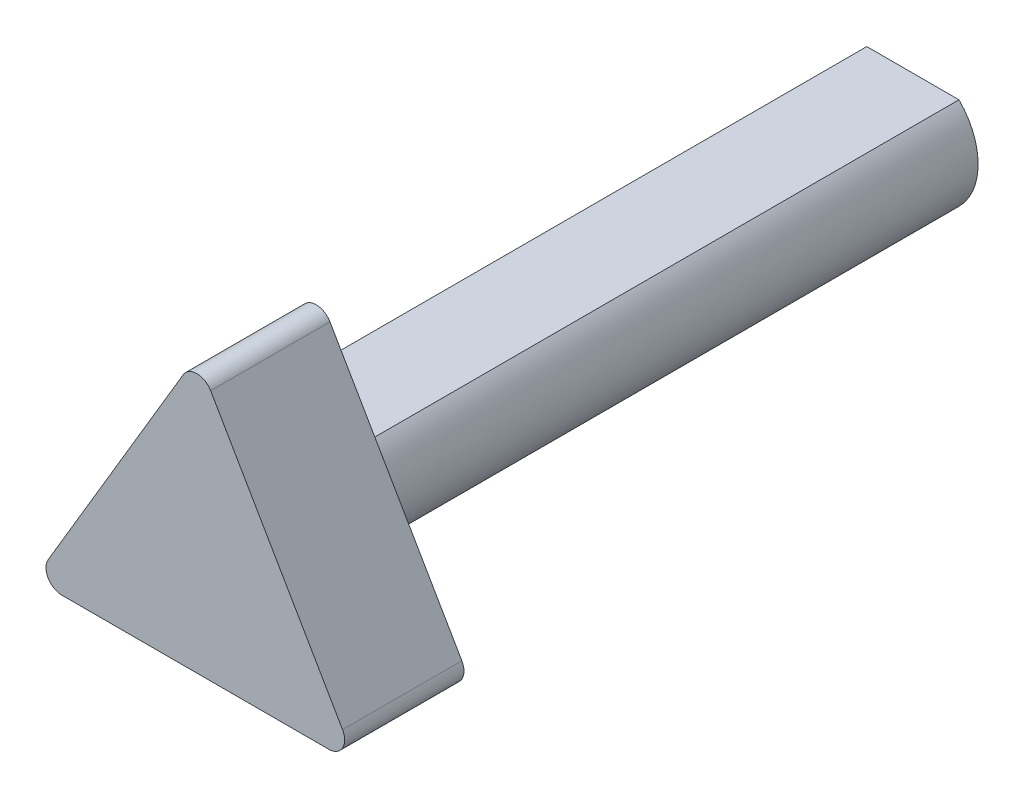
SolidWorks part; units mm, degrees
ref_plane "Front Plane" through (0, 0, 0) normal (0, 0, 1) x (1, 0, 0)
ref_plane "Top Plane" through (0, 0, 0) normal (0, 1, 0) x (1, 0, 0)
ref_plane "Right Plane" through (0, 0, 0) normal (1, 0, 0) x (0, 0, -1)
sketch "Sketch1" plane through (0, 0, 0) normal (0, 0, 1) x (1, 0, 0)
  line L1 (-7.3595, -7.3682) -> (7.3595, -7.3682)
  line L3 (-7.3595, 7.3682) -> (7.3595, 7.3682)
  arc A0 (-7.3595, 7.3682) -> (-7.3595, -7.3682) centre (0, 0) ccw
  arc A1 (7.3595, -7.3682) -> (7.3595, 7.3682) centre (0, 0) ccw
extrude "Boss-Extrude1" add sketch "Sketch1" against normal blind 114.3
sketch "Sketch2" plane through (0, 0, 0) normal (0, 0, 1) x (1, 0, 0)
  line L0 (0, 25.4394) -> (0, 0)
  line L1 (2.172, 21.6914) -> (23.2294, -14.6454)
  line L2 (21.0318, -18.4589) -> (-21.5826, -18.4589)
  line L3 (-23.7671, -14.6229) -> (-2.2102, 21.7138)
  arc A1 (-2.2102, 21.7138) -> (2.172, 21.6914) centre (-0.0257, 20.4179) cw
  arc A2 (-21.5826, -18.4589) -> (-23.7671, -14.6229) centre (-21.5826, -15.9189) cw
  arc A3 (23.2294, -14.6454) -> (21.0318, -18.4589) centre (21.0318, -15.9189) cw
  dimension "D1" = 2.54
  dimension "D2" = 2.54
  dimension "D3" = 2.54
extrude "Boss-Extrude2" add sketch "Sketch2" against normal blind 19.05
